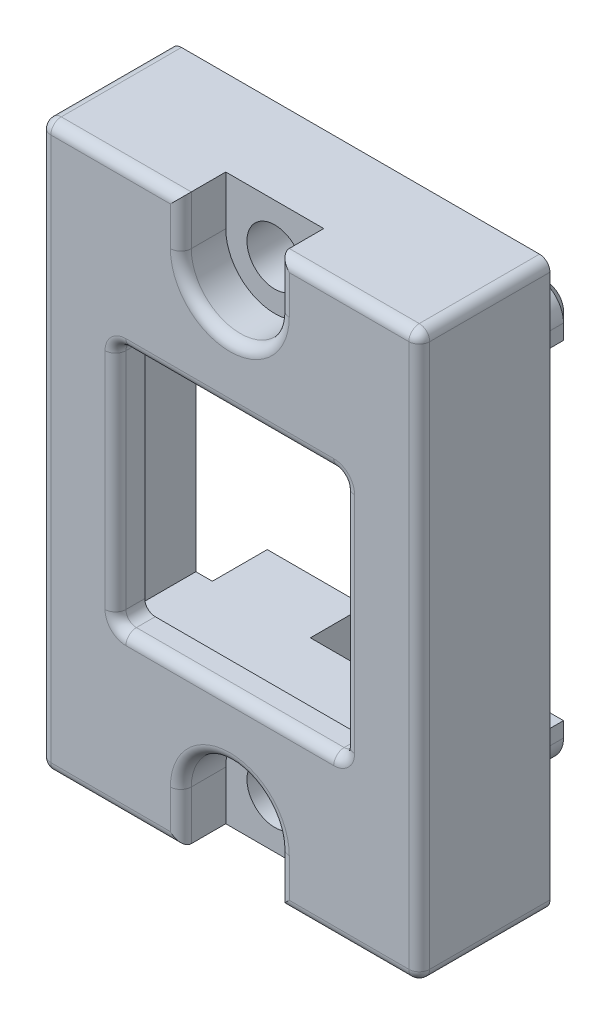
SolidWorks part; units mm, degrees
material "Nylon 101"
ref_plane "Front Plane" through (0, 0, 0) normal (0, 0, 1) x (1, 0, 0)
ref_plane "Top Plane" through (0, 0, 0) normal (0, 1, 0) x (1, 0, 0)
ref_plane "Right Plane" through (0, 0, 0) normal (1, 0, 0) x (0, 0, -1)
sketch "Sketch1" plane through (0, 0, 0) normal (0, 0, 1) x (1, 0, 0)
  line L0 (73.66, -84.3122) -> (64.4525, -84.3122) construction
  line L2 (82.8675, -98.0282) -> (82.8675, -70.5962)
  line L4 (64.4525, -98.0282) -> (64.4525, -70.5962)
  line L5 (82.8675, -98.0282) -> (64.4525, -70.5962) construction
  line L6 (82.8675, -70.5962) -> (64.4525, -98.0282) construction
  line L9 (64.4525, -70.5962) -> (82.8675, -70.5962)
  line L13 (64.4525, -98.0282) -> (82.8675, -98.0282)
  point P4 (73.66, -84.3122)
  point P6 (0, 0)
  point P7 (0, 0)
  point P10 (0, 0)
  point P14 (0, 0)
  point P15 (66.04, -71.7604)
  point P16 (0, 0)
  dimension "D1" = 27.432
  dimension "D2" = 18.415
extrude "Boss-Extrude1" add sketch "Sketch1" along normal blind 6.35
sketch "Sketch2" plane through (0, 0, 6.35) normal (0, 0, 1) x (1, 0, 0)
  line L5 (68.1037, -78.3591) -> (68.1037, -90.2654)
  line L6 (79.2162, -78.3591) -> (68.1037, -78.3591)
  line L7 (79.2162, -90.2654) -> (79.2162, -78.3591)
  line L8 (68.1037, -90.2654) -> (79.2162, -90.2654)
  line L9 (68.1037, -78.3591) -> (68.1037, -90.2654)
  line L10 (79.2162, -78.3591) -> (68.1037, -78.3591)
  line L11 (79.2162, -90.2654) -> (79.2162, -78.3591)
  line L12 (68.1037, -90.2654) -> (79.2162, -90.2654)
  dimension "D1" = 0
extrude "Cut-Extrude1" cut sketch "Sketch2" against normal through all
shell "Shell1" thickness 1
sketch "Sketch5" plane through (0, 0, 0) normal (0, 0, -1) x (-1, 0, 0)
  line L0 (-73.66, -98.0282) -> (-73.66, -70.5962) construction
  line L1 (-64.4525, -98.0282) -> (-82.8675, -98.0282) construction
  line L2 (-82.8675, -70.5962) -> (-64.4525, -70.5962) construction
  line L3 (-70.7724, -76.3714) -> (-70.7724, -70.5962)
  line L4 (-82.8675, -98.0282) -> (-82.8675, -70.5962) construction
  line L5 (-82.8675, -84.3122) -> (-73.66, -84.3122) construction
  line L6 (-76.5476, -92.253) -> (-70.7724, -92.253)
  line L7 (-76.5476, -92.253) -> (-76.5476, -98.0282)
  line L8 (-76.5476, -98.0282) -> (-70.7724, -98.0282)
  line L9 (-70.7724, -92.253) -> (-70.7724, -98.0282)
  line L10 (-76.5476, -92.253) -> (-70.7724, -98.0282) construction
  line L11 (-76.5476, -98.0282) -> (-70.7724, -92.253) construction
  line L12 (-76.5476, -76.3714) -> (-70.7724, -76.3714)
  line L13 (-76.5476, -76.3714) -> (-76.5476, -70.5962)
  line L14 (-76.5476, -70.5962) -> (-70.7724, -70.5962)
  point P6 (-73.66, -95.1406)
  dimension "D1" = 5.7752
extrude "Boss-Extrude2" add sketch "Sketch5" against normal through all
hole_wizard "CBORE for #2 Socket Head Cap Screw2" positions "Sketch4" profile "Sketch3" counterbore size "#2" standard "ANSI Inch" end condition through all
sketch "Sketch4" plane through (0, 0, 6.35) normal (0, 0, 1) x (1, 0, 0)
  line L0 (73.66, -70.5962) -> (73.66, -98.0282) construction
  line L1 (82.8675, -70.5962) -> (64.4525, -70.5962) construction
  line L2 (64.4525, -98.0282) -> (82.8675, -98.0282) construction
  line L3 (73.66, -84.3122) -> (82.8675, -84.3122) construction
  line L4 (82.8675, -98.0282) -> (82.8675, -70.5962) construction
  point P0 (73.66, -95.6406)
  point P23 (73.66, -72.9838)
  dimension "D1" = 2.3876
sketch "Sketch3" plane through (73.66, -95.6406, 6.35) normal (1, 0, 0) x (0, -1, 0)
  line L0 (0, 0) -> (0, 6.35)
  line L1 (0, 6.35) -> (1.3525, 6.35)
  line L3 (1.3525, 6.35) -> (1.3525, 2.1844)
  line L4 (1.3525, 2.1844) -> (2.3812, 2.1844)
  line L5 (2.3812, 2.1844) -> (2.3812, 0)
  line L7 (2.3812, 0) -> (0, 0)
  line L11 (0, -6.35) -> (0, 107.95) construction
  dimension "Thru Hole Dia." = 2.7051
  dimension "Thru Hole Depth" = 6.35
  dimension "C'Bore Dia." = 4.7625
  dimension "C'Bore Depth" = 2.1844
sketch "Sketch6" plane through (0, 0, 0) normal (0, 0, -1) x (-1, 0, 0)
  line L0 (-76.5476, -92.253) -> (-76.5476, -97.0282) construction
  line L1 (-76.5476, -95.6406) -> (-76.8016, -95.6406)
  line L2 (-76.8016, -95.6406) -> (-76.8016, -92.253)
  line L3 (-76.8016, -92.253) -> (-70.5184, -92.253)
  line L4 (-70.7724, -92.253) -> (-76.5476, -92.253) construction
  line L5 (-73.66, -95.6406) -> (-73.66, -92.753) construction
  line L6 (-70.7724, -95.6406) -> (-70.5184, -95.6406)
  line L7 (-70.5184, -95.6406) -> (-70.5184, -92.253)
  line L8 (-79.2162, -84.3122) -> (-68.1037, -84.3122) construction
  line L9 (-79.2162, -90.2654) -> (-79.2162, -78.3591) construction
  line L10 (-68.1037, -78.3591) -> (-68.1037, -90.2654) construction
  line L11 (-76.8016, -72.9838) -> (-76.8016, -76.3714)
  line L12 (-76.5476, -72.9838) -> (-76.8016, -72.9838)
  line L13 (-70.7724, -72.9838) -> (-70.5184, -72.9838)
  line L14 (-70.5184, -72.9838) -> (-70.5184, -76.3714)
  line L15 (-76.8016, -76.3714) -> (-70.5184, -76.3714)
  arc A1 (-70.7724, -95.6406) -> (-76.5476, -95.6406) centre (-73.66, -95.6406) ccw
  arc A2 (-70.7724, -72.9838) -> (-76.5476, -72.9838) centre (-73.66, -72.9838) cw
  point P15 (-73.66, -92.253)
  dimension "D1" = 0.254
extrude "Cut-Extrude2" cut sketch "Sketch6" against normal offset from surface (4.9276 mm away) 1.4224 up to face at (76.0413, -95.6406, 6.35)
sketch "Sketch7" plane through (0, 0, 5.35) normal (0, 0, -1) x (-1, 0, 0)
  line L4 (-79.2162, -90.2654) -> (-68.1037, -90.2654)
  line L5 (-79.2162, -78.3591) -> (-79.2162, -90.2654)
  line L6 (-68.1037, -78.3591) -> (-79.2162, -78.3591)
  line L7 (-68.1037, -90.2654) -> (-68.1037, -78.3591)
  line L8 (-79.2162, -90.2654) -> (-68.1037, -90.2654)
  line L9 (-79.2162, -78.3591) -> (-79.2162, -90.2654)
  line L10 (-68.1037, -78.3591) -> (-79.2162, -78.3591)
  line L11 (-68.1037, -90.2654) -> (-68.1037, -78.3591)
  line L12 (-70.7724, -76.3714) -> (-76.5476, -76.3714)
  line L13 (-76.5476, -76.3714) -> (-76.5476, -71.5962)
  line L14 (-76.5476, -71.5962) -> (-81.8675, -71.5962)
  line L15 (-81.8675, -71.5962) -> (-81.8675, -97.0282)
  line L16 (-81.8675, -97.0282) -> (-76.5476, -97.0282)
  line L17 (-76.5476, -97.0282) -> (-76.5476, -92.253)
  line L18 (-76.5476, -92.253) -> (-70.7724, -92.253)
  line L19 (-70.7724, -92.253) -> (-70.7724, -97.0282)
  line L20 (-70.7724, -97.0282) -> (-65.4525, -97.0282)
  line L21 (-65.4525, -97.0282) -> (-65.4525, -71.5962)
  line L22 (-65.4525, -71.5962) -> (-70.7724, -71.5962)
  line L23 (-70.7724, -71.5962) -> (-70.7724, -76.3714)
  line L24 (-70.7724, -76.3714) -> (-76.5476, -76.3714)
  line L25 (-76.5476, -76.3714) -> (-76.5476, -71.5962)
  line L26 (-76.5476, -71.5962) -> (-81.8675, -71.5962)
  line L27 (-81.8675, -71.5962) -> (-81.8675, -97.0282)
  line L28 (-81.8675, -97.0282) -> (-76.5476, -97.0282)
  line L29 (-76.5476, -97.0282) -> (-76.5476, -92.253)
  line L30 (-76.5476, -92.253) -> (-70.7724, -92.253)
  line L31 (-70.7724, -92.253) -> (-70.7724, -97.0282)
  line L32 (-70.7724, -97.0282) -> (-65.4525, -97.0282)
  line L33 (-65.4525, -97.0282) -> (-65.4525, -71.5962)
  line L34 (-65.4525, -71.5962) -> (-70.7724, -71.5962)
  line L35 (-70.7724, -71.5962) -> (-70.7724, -76.3714)
  dimension "D1" = 0
  dimension "D2" = 0
extrude "Boss-Extrude4" add sketch "Sketch7" along normal up to surface (0.4224 mm away) up to face at (73.66, -75.3995, 4.9276)
sketch "Sketch8" plane through (0, 0, 6.35) normal (0, 0, 1) x (1, 0, 0)
  line L0 (64.4525, -98.0282) -> (82.8675, -98.0282) construction
  line L1 (71.2788, -95.6406) -> (76.0413, -95.6406)
  line L2 (71.2788, -95.6406) -> (71.2788, -98.0282)
  line L3 (71.2788, -98.0282) -> (76.0413, -98.0282)
  line L4 (76.0413, -95.6406) -> (76.0413, -98.0282)
  line L5 (71.2788, -95.6406) -> (76.0413, -98.0282) construction
  line L6 (71.2788, -98.0282) -> (76.0413, -95.6406) construction
  line L7 (68.1037, -84.3122) -> (79.2162, -84.3122) construction
  line L8 (68.1037, -78.3591) -> (68.1037, -90.2654) construction
  line L9 (79.2162, -90.2654) -> (79.2162, -78.3591) construction
  line L10 (71.2788, -72.9838) -> (71.2788, -70.5962)
  line L11 (71.2788, -70.5962) -> (76.0413, -70.5962)
  line L12 (76.0413, -72.9838) -> (76.0413, -70.5962)
  line L13 (71.2788, -72.9838) -> (76.0413, -72.9838)
  circle A0 centre (73.66, -95.6406) radius 2.3813 construction
  point P4 (73.66, -96.8344)
  point P7 (73.66, -95.6406)
extrude "Cut-Extrude3" cut sketch "Sketch8" against normal up to surface (2.1844 mm away) up to face at (75.0125, -95.6406, 4.1656)
fillet "Fillet1" radius 0.508 24 edges at (79.2162, -84.3122, 6.35) (73.66, -78.3591, 6.35) (68.1037, -84.3122, 6.35) (73.66, -90.2654, 6.35) (79.4544, -70.5962, 6.35) (82.8675, -84.3122, 6.35) (79.4544, -98.0282, 6.35) (76.0413, -96.8344, 6.35) (73.66, -93.2594, 6.35) (71.2788, -96.8344, 6.35) (67.8656, -98.0282, 6.35) (64.4525, -84.3122, 6.35) (67.8656, -70.5962, 6.35) (71.2788, -71.79, 6.35) (73.66, -75.3651, 6.35) (76.0413, -71.79, 6.35) (64.4525, -98.0282, 3.175) (64.4525, -70.5962, 3.175) (82.8675, -70.5962, 3.175) (82.8675, -98.0282, 3.175) (68.1037, -78.3591, 5.6388) (79.2162, -78.3591, 5.6388) (79.2162, -90.2654, 5.6388) (68.1037, -90.2654, 5.6388)
sketch "Sketch10" plane through (0, 0, 0) normal (0, 0, -1) x (-1, 0, 0)
  line L0 (-73.66, -78.3591) -> (-73.66, -90.2654) construction
  line L1 (-78.7082, -78.3591) -> (-68.6117, -78.3591) construction
  line L2 (-68.6117, -90.2654) -> (-78.7082, -90.2654) construction
  line L4 (-65.66, -92.3122) -> (-81.66, -92.3122)
  line L5 (-65.66, -92.3122) -> (-65.66, -76.3122)
  line L6 (-65.66, -76.3122) -> (-81.66, -76.3122)
  line L7 (-81.66, -92.3122) -> (-81.66, -76.3122)
  line L8 (-65.66, -92.3122) -> (-81.66, -76.3122) construction
  line L9 (-65.66, -76.3122) -> (-81.66, -92.3122) construction
  line L19 (-76.5476, -97.0282) -> (-76.5476, -95.6406)
  line L20 (-70.7724, -95.6406) -> (-70.7724, -97.0282)
  line L21 (-70.7724, -97.0282) -> (-65.4525, -97.0282)
  line L22 (-65.4525, -97.0282) -> (-65.4525, -71.5962)
  line L23 (-65.4525, -71.5962) -> (-70.7724, -71.5962)
  line L24 (-70.7724, -71.5962) -> (-70.7724, -72.9838)
  line L25 (-76.5476, -72.9838) -> (-76.5476, -71.5962)
  line L26 (-76.5476, -71.5962) -> (-81.8675, -71.5962)
  line L27 (-81.8675, -71.5962) -> (-81.8675, -97.0282)
  line L28 (-81.8675, -97.0282) -> (-76.5476, -97.0282)
  line L29 (-76.5476, -97.0282) -> (-76.5476, -95.6406)
  line L30 (-70.7724, -95.6406) -> (-70.7724, -97.0282)
  line L31 (-70.7724, -97.0282) -> (-65.4525, -97.0282)
  line L32 (-65.4525, -97.0282) -> (-65.4525, -71.5962)
  line L33 (-65.4525, -71.5962) -> (-70.7724, -71.5962)
  line L34 (-70.7724, -71.5962) -> (-70.7724, -72.9838)
  line L35 (-76.5476, -72.9838) -> (-76.5476, -71.5962)
  line L36 (-76.5476, -71.5962) -> (-81.8675, -71.5962)
  line L37 (-81.8675, -71.5962) -> (-81.8675, -97.0282)
  line L38 (-81.8675, -97.0282) -> (-76.5476, -97.0282)
  arc A2 (-70.7724, -95.6406) -> (-76.5476, -95.6406) centre (-73.66, -95.6406) ccw
  arc A3 (-76.5476, -72.9838) -> (-70.7724, -72.9838) centre (-73.66, -72.9838) ccw
  arc A4 (-70.7724, -95.6406) -> (-76.5476, -95.6406) centre (-73.66, -95.6406) ccw
  arc A5 (-76.5476, -72.9838) -> (-70.7724, -72.9838) centre (-73.66, -72.9838) ccw
  point P6 (-73.66, -84.3122)
  dimension "D1" = 16
  dimension "D2" = 0
extrude "Boss-Extrude5" add sketch "Sketch10" against normal up to next
sketch "Sketch11" plane through (0, 0, 0) normal (0, 0, -1) x (-1, 0, 0)
  line L0 (-67.795, -94.6322) -> (-71.224, -94.6322) construction
  line L2 (-81.66, -92.3122) -> (-65.66, -92.3122) construction
  line L4 (-81.66, -92.3122) -> (-65.66, -92.3122) construction
  line L5 (-66.2075, -92.3122) -> (-66.2075, -93.0447) construction
  line L6 (-66.4615, -92.3122) -> (-66.4615, -93.0447)
  line L7 (-67.795, -94.3782) -> (-71.224, -94.3782)
  line L8 (-71.224, -94.3782) -> (-71.224, -92.3122)
  line L9 (-71.224, -92.3122) -> (-66.4615, -92.3122)
  line L10 (-73.66, -76.3122) -> (-73.66, -92.3122) construction
  line L11 (-65.66, -76.3122) -> (-81.66, -76.3122) construction
  line L12 (-73.66, -84.3122) -> (-65.66, -84.3122) construction
  line L13 (-65.66, -92.3122) -> (-65.66, -76.3122) construction
  line L14 (-76.096, -92.3122) -> (-80.8585, -92.3122)
  line L15 (-76.096, -94.3782) -> (-76.096, -92.3122)
  line L16 (-79.525, -94.3782) -> (-76.096, -94.3782)
  line L17 (-80.8585, -92.3122) -> (-80.8585, -93.0447)
  line L18 (-80.8585, -76.3122) -> (-80.8585, -75.5797)
  line L19 (-79.525, -74.2462) -> (-76.096, -74.2462)
  line L20 (-76.096, -74.2462) -> (-76.096, -76.3122)
  line L21 (-76.096, -76.3122) -> (-80.8585, -76.3122)
  line L22 (-71.224, -76.3122) -> (-66.4615, -76.3122)
  line L23 (-71.224, -74.2462) -> (-71.224, -76.3122)
  line L24 (-67.795, -74.2462) -> (-71.224, -74.2462)
  line L25 (-66.4615, -76.3122) -> (-66.4615, -75.5797)
  arc A0 (-66.2075, -93.0447) -> (-67.795, -94.6322) centre (-67.795, -93.0447) cw construction
  arc A1 (-66.4615, -93.0447) -> (-67.795, -94.3782) centre (-67.795, -93.0447) cw
  arc A2 (-80.8585, -93.0447) -> (-79.525, -94.3782) centre (-79.525, -93.0447) ccw
  arc A3 (-80.8585, -75.5797) -> (-79.525, -74.2462) centre (-79.525, -75.5797) cw
  arc A4 (-66.4615, -75.5797) -> (-67.795, -74.2462) centre (-67.795, -75.5797) ccw
  point P14 (-66.6724, -94.1673)
  dimension "D2" = 4.7625
  dimension "D1" = 0.254
extrude "Boss-Extrude6" add sketch "Sketch11" along normal blind 3.175
chamfer "Chamfer1" distance 0.508 angle 45 20 edges at (68.8427, -76.3122, -3.175) (71.224, -75.2792, -3.175) (69.5095, -74.2462, -3.175) (66.852, -74.6368, -3.175) (66.4615, -75.946, -3.175) (77.8105, -74.2462, -3.175) (76.096, -75.2792, -3.175) (78.4773, -76.3122, -3.175) (80.8585, -75.946, -3.175) (80.468, -74.6368, -3.175) (78.4773, -92.3122, -3.175) (76.096, -93.3452, -3.175) (77.8105, -94.3782, -3.175) (80.468, -93.9877, -3.175) (80.8585, -92.6785, -3.175) (66.4615, -92.6785, -3.175) (66.852, -93.9877, -3.175) (69.5095, -94.3782, -3.175) (71.224, -93.3452, -3.175) (68.8427, -92.3122, -3.175)
